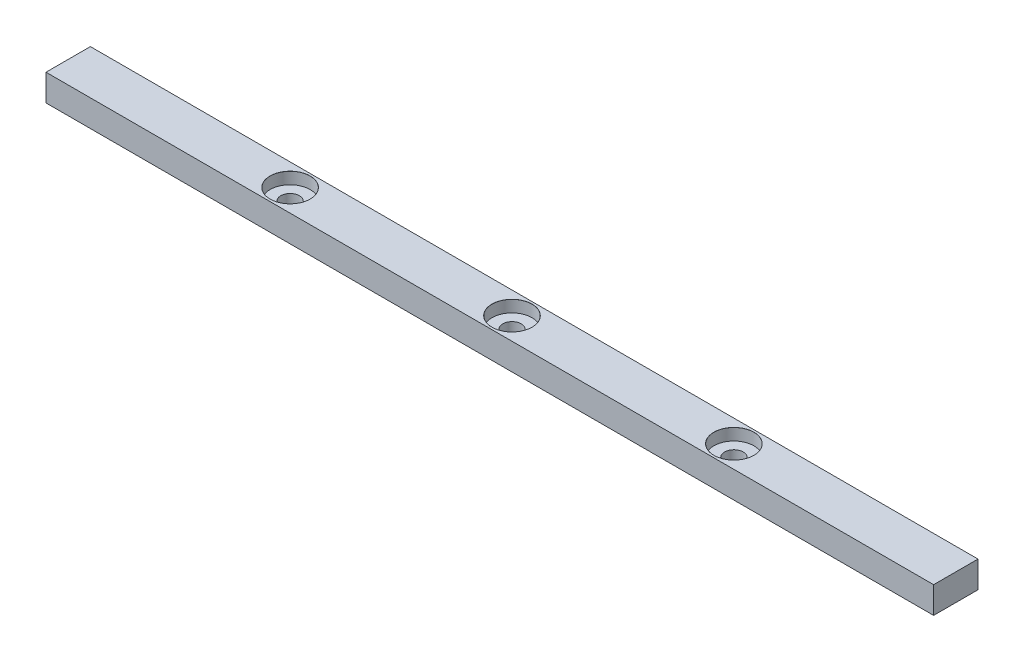
SolidWorks part; units mm, degrees
other "Markup1"
sketch "Sketch3" plane through (200, 12, -10) normal (0.0517, 0.859, -0.5094) x (0.9957, -0.0837, -0.0402)
ref_plane "Front Plane" through (0, 0, 0) normal (0, 0, 1) x (1, 0, 0)
ref_plane "Top Plane" through (0, 0, 0) normal (0, 1, 0) x (1, 0, 0)
ref_plane "Right Plane" through (0, 0, 0) normal (1, 0, 0) x (0, 0, -1)
sketch "Sketch1" plane through (0, 0, 0) normal (0, 1, 0) x (1, 0, 0)
  line L1 (-200, -10) -> (200, -10)
  line L2 (-200, -10) -> (-200, 10)
  line L3 (-200, 10) -> (200, 10)
  line L4 (200, -10) -> (200, 10)
  line L5 (-200, -10) -> (200, 10) construction
  line L6 (-200, 10) -> (200, -10) construction
  point P0 (0, 0)
  dimension "D1" = 400
  dimension "D2" = 20
extrude "Boss-Extrude1" add sketch "Sketch1" along normal blind 12
sketch "Sketch2" plane through (0, 12, 0) normal (0, 1, 0) x (1, 0, 0)
  circle A0 centre (-100, 0) radius 6
  circle A1 centre (0, 0) radius 6
  circle A2 centre (100, 0) radius 6
hole_wizard "CBORE for M8 Hex Head Bolt1" positions "3DSketch2" profile "Sketch5" counterbore size "M8" standard "ISO" end condition through all
sketch3d "3DSketch2"
  point P0 (0, 12, 0)
  point P3 (100, 12, 0)
  point P6 (-100, 12, 0)
sketch "Sketch5" plane through (0, 12, 0) normal (1, 0, 0) x (0, 0, 1)
  line L0 (0, 0) -> (0, 12)
  line L1 (0, 12) -> (4.2, 12)
  line L3 (4.2, 12) -> (4.2, 5.3)
  line L4 (9.0055, 5.3) -> (4.2, 5.3)
  line L5 (9.0055, 5.3) -> (9.0055, 0.025)
  line L6 (9.0055, 0.025) -> (9.0305, 0)
  line L7 (9.0305, 0) -> (0, 0)
  line L8 (-9.0055, 0.025) -> (-9.0305, 0) construction
  line L11 (0, -6.35) -> (0, 107.95) construction
  dimension "Thru Hole Dia." = 8.4
  dimension "Thru Hole Depth" = 12
  dimension "C'Bore Dia." = 18.011
  dimension "C'Bore Depth" = 5.3
  dimension "Near C'Sink Dia." = 18.061
  dimension "Near C'Sink Angle" = 90
